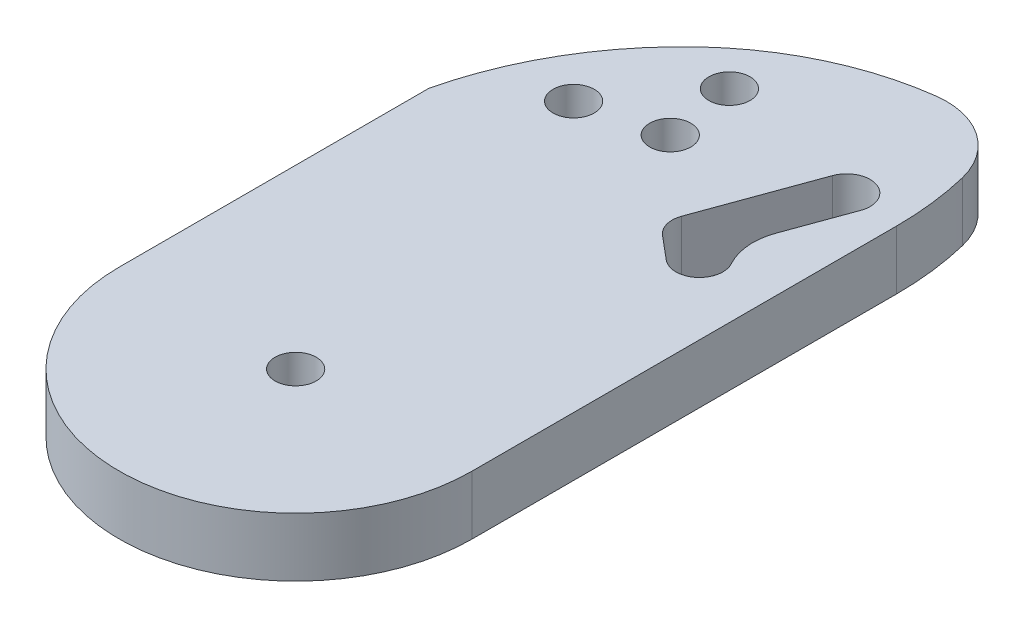
SolidWorks part; units mm, degrees
ref_plane "Front Plane" through (0, 0, 0) normal (0, 0, 1) x (1, 0, 0)
ref_plane "Top Plane" through (0, 0, 0) normal (0, 1, 0) x (1, 0, 0)
ref_plane "Right Plane" through (0, 0, 0) normal (1, 0, 0) x (0, 0, -1)
sketch "Sketch1" plane through (0, 0, 0) normal (0, 1, 0) x (1, 0, 0)
  line L0 (0, 0) -> (0, 50) construction
  line L1 (-15, 0) -> (-15, 50)
  line L2 (15, 0) -> (15, 50)
  line L3 (10.4451, 36.3547) -> (7.0249, 26.9578) construction
  line L4 (12.3245, 35.6707) -> (9.3833, 27.5897)
  line L5 (8.5657, 37.0388) -> (5.1455, 27.6419)
  line L6 (0, 65) -> (0, 60) construction
  line L7 (0, 60) -> (-6.5, 48.7417) construction
  line L8 (-6.5, 48.7417) -> (6.5, 48.7417) construction
  line L9 (6.5, 48.7417) -> (0, 60) construction
  line L10 (7.0249, 26.9578) -> (9, 25.3005) construction
  line L11 (9.3833, 27.5897) -> (10.2856, 26.8326)
  line L12 (5.7393, 25.4257) -> (7.7144, 23.7684)
  arc A0 (-15, 0) -> (15, 0) centre (0, 0) ccw
  arc A1 (15, 50) -> (-15, 50) centre (0, 50) ccw
  circle A2 centre (0, 0) radius 1.75
  arc A3 (12.3245, 35.6707) -> (8.5657, 37.0388) centre (10.4451, 36.3547) ccw
  arc A4 (5.1455, 27.6419) -> (5.7393, 25.4257) centre (7.0249, 26.9578) ccw
  circle A5 centre (0, 60) radius 3.175 construction
  circle A6 centre (-6.5, 48.7417) radius 3.175 construction
  circle A7 centre (6.5, 48.7417) radius 3.175 construction
  arc A9 (5.1455, 27.6419) -> (5.7393, 25.4257) centre (7.0249, 26.9578) ccw
  arc A10 (7.7144, 23.7684) -> (10.2856, 26.8326) centre (9, 25.3005) ccw
  point P3 (0, 25)
  point P12 (6.2189, 27.2917)
  point P24 (5.4964, 12.8256)
  dimension "D1" = 15
  dimension "D2" = 3.5
  dimension "D4" = 2
  dimension "D7" = 6.35
  dimension "D8" = 5
  dimension "D12" = 110
  dimension "D3" = 50
  dimension "D5" = 20
  dimension "D6" = 10
  dimension "D9" = 13
  dimension "D10" = 13
  dimension "D11" = 6
  dimension "D13" = 13.6453
extrude "Boss-Extrude1" add sketch "Sketch1" along normal blind 5 contours L2 A1 L1 A0 A10 L12 A4 L5 A3 L4 L11 A7 A6 A5 A2
fillet "Fillet1" radius 5 1 edges at (9.3833, 2.5, -27.5897)
sketch "Sketch2" plane through (0, 5, 0) normal (0, 1, 0) x (1, 0, 0)
  line L0 (15, 0) -> (15, 50) construction
  line L2 (-15, 0) -> (-15, 50) construction
  line L3 (-15, 26.3246) -> (-40.9256, 69.2382)
  line L4 (-40.9256, 69.2382) -> (-58.772, 111.0807)
  line L5 (-58.772, 111.0807) -> (39.2844, 102.8258)
  line L6 (39.2844, 102.8258) -> (15, 36.047)
  arc A0 (15, 36.047) -> (14.2432, 42.3998) centre (-12.0434, 36.047) ccw
  arc A1 (14.2432, 42.3998) -> (7.1271, 47.2922) centre (7.9593, 40.8811) ccw
  arc A2 (7.1271, 47.2922) -> (-6.484, 40.9149) centre (10.3077, 22.7899) ccw
  arc A3 (-6.484, 40.9149) -> (-15, 26.3246) centre (13.2458, 19.6186) ccw
extrude "Cut-Extrude1" cut sketch "Sketch2" against normal blind 10
sketch "Sketch3" plane through (0, 5, 0) normal (0, 1, 0) x (1, 0, 0)
  circle A0 centre (6.1014, 47.3659) radius 3.81 construction
  circle A1 centre (-1.3018, 33.1261) radius 1.75
  circle A2 centre (3.3822, 36.8758) radius 1.75 construction
  circle A3 centre (-2.2071, 39.0574) radius 1.75
  circle A4 centre (-7.9059, 31.5198) radius 1.75
  dimension "D1" = 7.62
  dimension "D2" = 3.5
  dimension "D7" = 3.5
  dimension "D3" = 10
  dimension "D4" = 6
  dimension "D5" = 6
  dimension "D6" = 6
extrude "Cut-Extrude2" cut sketch "Sketch3" against normal blind 10
